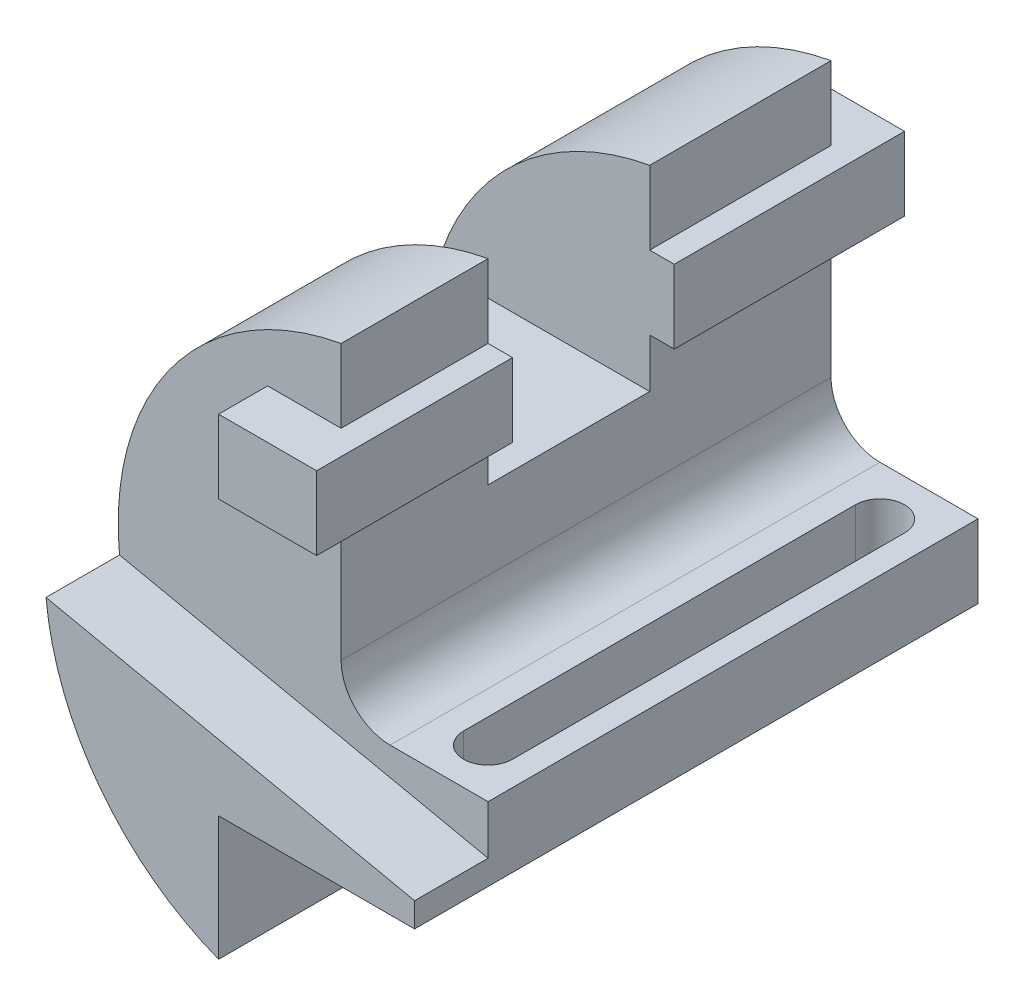
SolidWorks part; units mm, degrees
material "1060 Alloy"
ref_plane "Front Plane" through (0, 0, 0) normal (0, 0, 1) x (1, 0, 0)
ref_plane "Top Plane" through (0, 0, 0) normal (0, 1, 0) x (1, 0, 0)
ref_plane "Right Plane" through (0, 0, 0) normal (1, 0, 0) x (0, 0, -1)
sketch "Sketch1" plane through (0, 0, 0) normal (0, 0, 1) x (1, 0, 0)
  line L0 (-10, 54.5917) -> (-10, -1.4083)
  line L1 (0, -11.4083) -> (20, -11.4083)
  line L2 (20, -11.4083) -> (20, -26.4083)
  line L3 (20, -26.4083) -> (-20, -26.4083)
  line L4 (-20, -26.4083) -> (-20, -51.7711)
  arc A0 (-10, 54.5917) -> (-20, -51.7711) centre (0, 0) ccw
  arc A1 (0, -11.4083) -> (-10, -1.4083) centre (0, -1.4083) cw
  dimension "D4" = 10
  dimension "D5" = 55.5
  dimension "D1" = 40
  dimension "D2" = 10
  dimension "D3" = 20
  dimension "D6" = 15
  dimension "D7" = 66
extrude "Boss-Extrude1" add sketch "Sketch1" along normal blind 100
sketch "Sketch2" plane through (-10, 0, 0) normal (1, 0, 0) x (0, 0, -1)
  line L0 (-100, 54.5917) -> (0, 54.5917) construction
  line L1 (-70, 54.5917) -> (-37, 54.5917)
  line L2 (-70, 54.5917) -> (-70, 14.5917)
  line L3 (-70, 14.5917) -> (-37, 14.5917)
  line L4 (-37, 54.5917) -> (-37, 14.5917)
  line L5 (-100, -1.4083) -> (-100, 54.5917) construction
  dimension "D1" = 33
  dimension "D2" = 30
  dimension "D3" = 40
extrude "Cut-Extrude1" cut sketch "Sketch2" against normal through all
sketch "Sketch3" plane through (0, 0, 37) normal (0, 0, 1) x (1, 0, 0)
  line L0 (-10, -1.4083) -> (-10, 54.5917) construction
  line L1 (-25, 39.5917) -> (-5, 39.5917)
  line L2 (-25, 39.5917) -> (-25, 24.5917)
  line L3 (-25, 24.5917) -> (-5, 24.5917)
  line L4 (-5, 39.5917) -> (-5, 24.5917)
  dimension "D1" = 5
  dimension "D2" = 15
  dimension "D3" = 15
  dimension "D4" = 20
extrude "Boss-Extrude2" add sketch "Sketch3" against normal blind 47
sketch "Sketch5" plane through (0, 0, 70) normal (0, 0, -1) x (-1, 0, 0)
  line L1 (5, 39.5917) -> (25, 39.5917)
  line L2 (5, 39.5917) -> (5, 24.5917)
  line L3 (5, 24.5917) -> (25, 24.5917)
  line L4 (25, 39.5917) -> (25, 24.5917)
extrude "Boss-Extrude3" add sketch "Sketch5" against normal blind 40
sketch "Sketch6" plane through (0, -11.4083, 0) normal (0, 1, 0) x (1, 0, 0)
  line L0 (10, -10) -> (10, -90) construction
  line L1 (15, -10) -> (15, -90)
  line L2 (5, -10) -> (5, -90)
  line L3 (20, 0) -> (0, 0) construction
  line L4 (20, -100) -> (0, -100) construction
  line L5 (20, -100) -> (20, 0) construction
  arc A0 (15, -10) -> (5, -10) centre (10, -10) ccw
  arc A1 (5, -90) -> (15, -90) centre (10, -90) ccw
  point P2 (10, -50)
  dimension "D1" = 10
  dimension "D2" = 80
  dimension "D3" = 10
  dimension "D4" = 10
  dimension "D5" = 10
extrude "Cut-Extrude2" cut sketch "Sketch6" against normal up to next
sketch "Sketch7" plane through (0, 0, 100) normal (0, 0, 1) x (1, 0, 0)
  line L0 (20, -21.4083) -> (-55.235, -5.4166)
  line L1 (20, -26.4083) -> (20, -11.4083) construction
  line L2 (-20, -26.4083) -> (20, -26.4083) construction
  line L3 (-20, -51.7711) -> (-20, -26.4083) construction
  line L4 (20, -21.4083) -> (20, -26.4083)
  line L5 (-20, -26.4083) -> (20, -26.4083)
  line L6 (-20, -51.7711) -> (-20, -26.4083)
  arc A0 (-10, 54.5917) -> (-20, -51.7711) centre (0, 0) ccw construction
  arc A1 (-55.235, -5.4166) -> (-20, -51.7711) centre (0, 0) ccw
  dimension "D1" = 78
  dimension "D2" = 5
extrude "Boss-Extrude4" add sketch "Sketch7" along normal blind 15
equation "\"A\"= 55.5"
equation "\"B\"= 66"
equation "\"C\"= 33"
equation "\"D5@Sketch1\"=\"A\""
equation "\"D7@Sketch1\"=\"B\""
equation "\"D1@Sketch2\"=\"C\""
